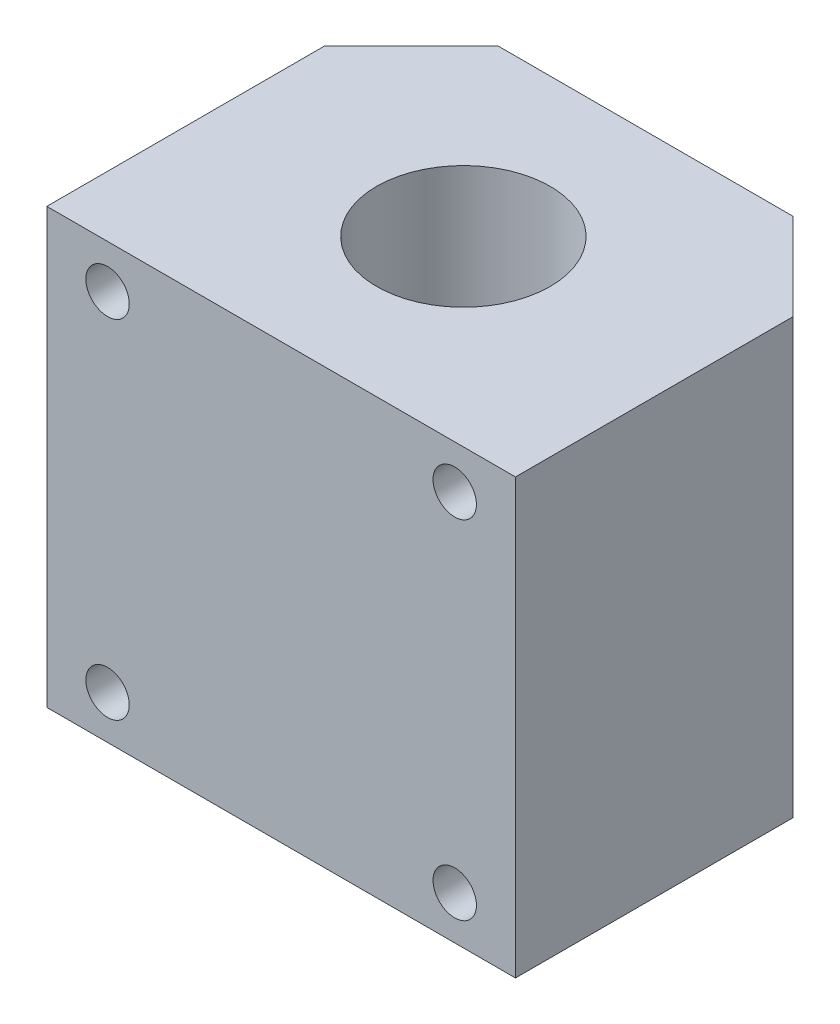
SolidWorks part; units mm, degrees
ref_plane "Front Plane" through (0, 0, 0) normal (0, 0, 1) x (1, 0, 0)
ref_plane "Top Plane" through (0, 0, 0) normal (0, 1, 0) x (1, 0, 0)
ref_plane "Right Plane" through (0, 0, 0) normal (1, 0, 0) x (0, 0, -1)
sketch "Sketch1" plane through (0, 0, 0) normal (0, 0, 1) x (1, 0, 0)
  line L1 (27, -25) -> (-27, -25)
  line L2 (27, -25) -> (27, 25)
  line L3 (27, 25) -> (-27, 25)
  line L4 (-27, -25) -> (-27, 25)
  line L5 (27, -25) -> (-27, 25) construction
  line L6 (27, 25) -> (-27, -25) construction
  point P0 (0, 0)
  dimension "D1" = 54
  dimension "D2" = 50
extrude "Boss-Extrude1" add sketch "Sketch1" along normal blind 42
chamfer "Chamfer1" distance 10 angle 45 2 edges at (27, 0, 0) (-27, 0, 0)
sketch "Sketch2" plane through (0, 25, 0) normal (0, 1, 0) x (1, 0, 0)
  line L0 (-27, -21) -> (27, -21) construction
  line L1 (-27, -42) -> (-27, -10) construction
  line L2 (27, -42) -> (27, -10) construction
  line L3 (27, -42) -> (-27, -42) construction
  circle A0 centre (0, -21) radius 10
  dimension "D1" = 20
  dimension "D2" = 21
extrude "Cut-Extrude1" cut sketch "Sketch2" against normal through all
sketch "Sketch3" plane through (0, 0, 42) normal (0, 0, 1) x (1, 0, 0)
  line L1 (20, -20) -> (-20, -20) construction
  line L2 (20, -20) -> (20, 20) construction
  line L3 (20, 20) -> (-20, 20) construction
  line L4 (-20, -20) -> (-20, 20) construction
  line L5 (20, -20) -> (-20, 20) construction
  line L6 (20, 20) -> (-20, -20) construction
  circle A0 centre (-20, 20) radius 2.5
  circle A1 centre (20, 20) radius 2.5
  circle A2 centre (-20, -20) radius 2.5
  circle A3 centre (20, -20) radius 2.5
  point P8 (0, 0)
  dimension "D1" = 5
  dimension "D2" = 40
  dimension "D3" = 40
extrude "Cut-Extrude2" cut sketch "Sketch3" against normal blind 15
